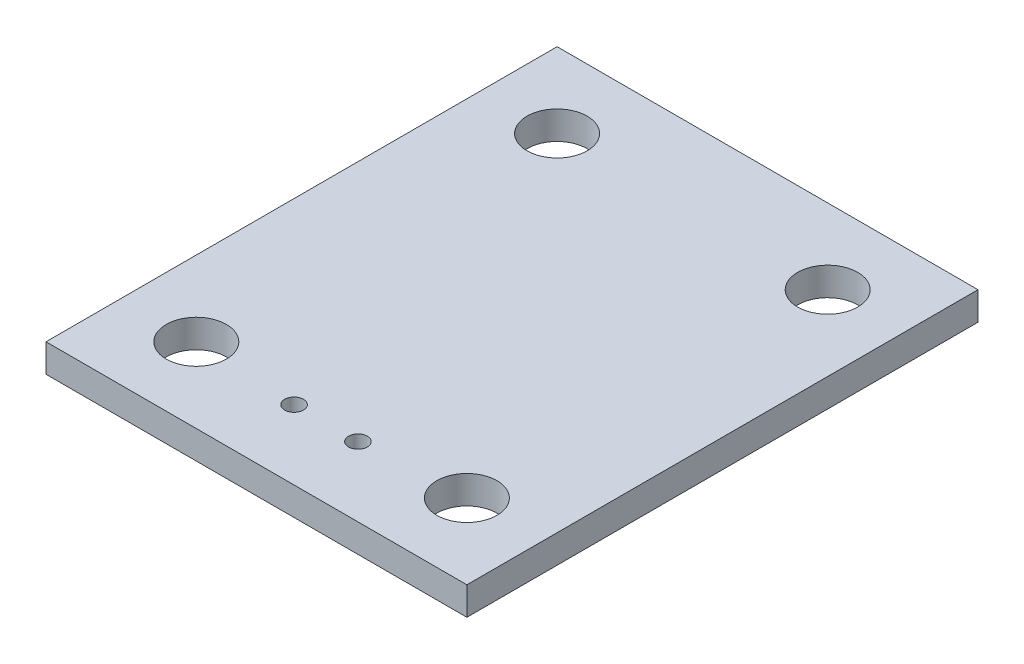
SolidWorks part; units mm, degrees
ref_plane "Front Plane" through (0, 0, 0) normal (0, 0, 1) x (1, 0, 0)
ref_plane "Top Plane" through (0, 0, 0) normal (0, 1, 0) x (1, 0, 0)
ref_plane "Right Plane" through (0, 0, 0) normal (1, 0, 0) x (0, 0, -1)
sketch "Sketch1" plane through (0, 0, 0) normal (0, 1, 0) x (1, 0, 0)
  line L0 (0, 13.6) -> (0, 0) construction
  line L1 (-11.2, 13.6) -> (11.2, 13.6)
  line L2 (-11.2, 13.6) -> (-11.2, -13.6)
  line L3 (-11.2, -13.6) -> (11.2, -13.6)
  line L4 (11.2, 13.6) -> (11.2, -13.6)
  line L5 (0, 0) -> (11.2, 0) construction
  line L6 (11.2, -13.6) -> (11.2, 13.6) construction
  line L7 (11.2, 13.6) -> (-11.2, 13.6) construction
  circle A0 centre (7.2, 9.6) radius 1.6
  circle A1 centre (-7.2, 9.6) radius 1.6
  circle A2 centre (-7.2, -9.6) radius 1.6
  circle A3 centre (-1.7, -9.9) radius 0.5
  circle A4 centre (1.7, -9.9) radius 0.5
  circle A5 centre (7.2, -9.6) radius 1.6
  circle A6 centre (7.2, -9.6) radius 1.6 construction
  circle A7 centre (1.7, -9.9) radius 0.5 construction
  circle A8 centre (-1.7, -9.9) radius 0.5 construction
  circle A9 centre (-7.2, -9.6) radius 1.6 construction
  circle A10 centre (-7.2, 9.6) radius 1.6 construction
  circle A11 centre (7.2, 9.6) radius 1.6 construction
extrude "Boss-Extrude1" add sketch "Sketch1" against normal blind 1.5
sketch "Sketch2" plane through (0, 0, 0) normal (0, 1, 0) x (1, 0, 0)
  line L0 (3.2, -6.2) -> (3.2, -3.8)
  line L1 (3.2, -3.8) -> (0.2, -3.8)
  line L2 (0.2, -3.8) -> (0.2, -6.2)
  line L3 (0.2, -6.2) -> (3.2, -6.2)
  line L4 (-0.2, -6.2) -> (-0.2, -3.8)
  line L5 (-0.2, -3.8) -> (-3.2, -3.8)
  line L6 (-3.2, -3.8) -> (-3.2, -6.2)
  line L7 (-3.2, -6.2) -> (-0.2, -6.2)
  line L8 (3.2, 3.8) -> (3.2, 6.2)
  line L9 (3.2, 6.2) -> (0.2, 6.2)
  line L10 (0.2, 6.2) -> (0.2, 3.8)
  line L11 (0.2, 3.8) -> (3.2, 3.8)
  line L12 (-0.2, 3.8) -> (-0.2, 6.2)
  line L13 (-0.2, 6.2) -> (-3.2, 6.2)
  line L14 (-3.2, 6.2) -> (-3.2, 3.8)
  line L15 (-3.2, 3.8) -> (-0.2, 3.8)
